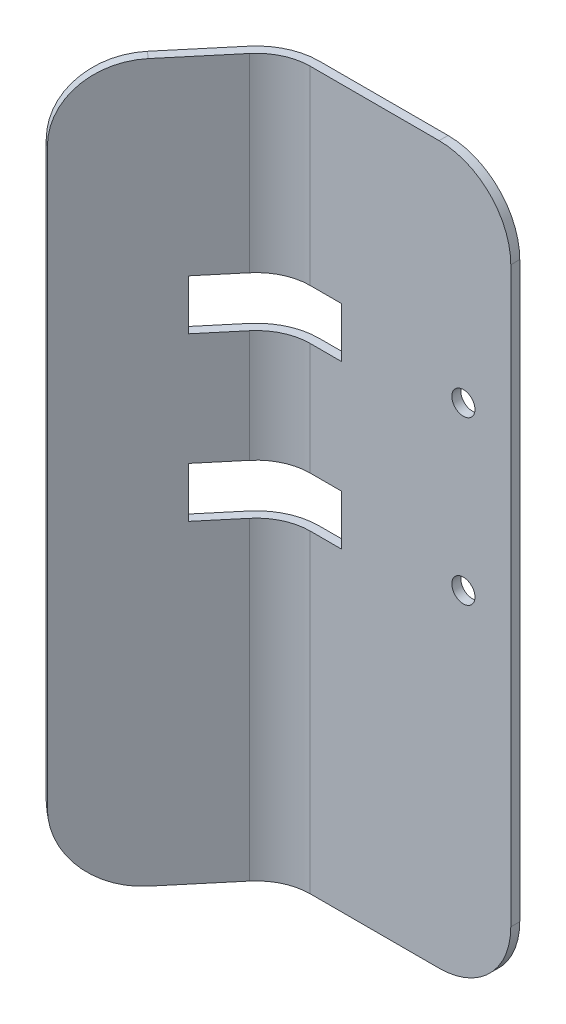
SolidWorks part; units mm, degrees
ref_plane "Front Plane" through (0, 0, 0) normal (0, 0, 1) x (1, 0, 0)
ref_plane "Top Plane" through (0, 0, 0) normal (0, 1, 0) x (1, 0, 0)
ref_plane "Right Plane" through (0, 0, 0) normal (1, 0, 0) x (0, 0, -1)
other "Bounding Box"
ref_plane "Default Plane" through (13.8565, 3.175, 6.7999) normal (0, -1, 0) x (-1, 0, 0)
sketch "Sketch1" plane through (0, 0, 0) normal (0, 1, 0) x (1, 0, 0)
  line L0 (0, 0) -> (-35.56, 0)
  line L1 (-42.8566, -3.4024) -> (-59.217, -22.9)
  line L2 (0, 1.5875) -> (-35.56, 1.5875)
  line L3 (-44.0727, -2.382) -> (-60.4331, -21.8796)
  line L4 (-60.4331, -21.8796) -> (-59.217, -22.9)
  line L5 (0, 1.5875) -> (0, 0)
  arc A0 (-35.56, 0) -> (-42.8566, -3.4024) centre (-35.56, -9.525) ccw
  arc A1 (-35.56, 1.5875) -> (-44.0727, -2.382) centre (-35.56, -9.525) ccw
  point P11 (-64.9523, -7.3771)
  point P12 (-61.4052, -4.5354)
  dimension "D5" = 9.525
  dimension "D2" = 35.56
  dimension "D3" = 22.9
  dimension "D4" = 130
  dimension "D1" = 1.5875
extrude "Boss-Extrude1" add sketch "Sketch1" along normal blind 127
sketch "Sketch2" plane through (0, 0, -1.5875) normal (0, 0, -1) x (-1, 0, 0)
  line L0 (8.4, 60.1161) -> (8.4, 88.9) construction
  line L1 (8.4, 88.9) -> (40.4616, 88.9) construction
  line L2 (40.4616, 88.9) -> (40.4616, 60.1161) construction
  line L3 (40.4616, 60.1161) -> (8.4, 60.1161) construction
  line L7 (0, 127) -> (35.56, 127) construction
  line L9 (0, 127) -> (0, 0) construction
  line L11 (29.99, 84.455) -> (49.04, 84.455)
  line L12 (29.99, 84.455) -> (29.99, 93.345)
  line L13 (29.99, 93.345) -> (49.04, 93.345)
  line L14 (49.04, 84.455) -> (49.04, 93.345)
  line L15 (29.99, 84.455) -> (49.04, 93.345) construction
  line L16 (29.99, 93.345) -> (49.04, 84.455) construction
  line L17 (29.99, 55.6711) -> (49.04, 55.6711)
  line L18 (29.99, 55.6711) -> (29.99, 64.5611)
  line L19 (29.99, 64.5611) -> (49.04, 64.5611)
  line L20 (49.04, 55.6711) -> (49.04, 64.5611)
  line L21 (29.99, 55.6711) -> (49.04, 64.5611) construction
  line L22 (29.99, 64.5611) -> (49.04, 55.6711) construction
  circle A0 centre (40.4616, 60.1161) radius 2.05 construction
  circle A1 centre (40.4616, 88.9) radius 2.05 construction
  circle A2 centre (8.4, 88.9) radius 2.05
  circle A3 centre (8.4, 60.1161) radius 2.05
  point P12 (39.515, 88.9)
  point P17 (39.515, 60.1161)
  point P22 (24.8584, 47.4161)
  point P23 (19.1648, 72.5709)
  dimension "D3" = 4.1
  dimension "D1" = 28.7839
  dimension "D2" = 32.0616
  dimension "D4" = 38.1
  dimension "D5" = 6.35
  dimension "D6" = 8.89
  dimension "D8" = 19.05
  dimension "D7" = 21.59
extrude "Cut-Extrude1" cut sketch "Sketch2" against normal through all
fillet "Fillet1" radius 12.7 4 edges at (-59.825, 127, 22.3898) (-59.825, 0, 22.3898) (0, 127, -0.7937) (0, 0, -0.7937)
sketch "Sketch4" plane through (-23.4739, 0, -19.6969) normal (0.766, 0, 0.6428) x (0.6428, 0, -0.766)
  line L0 (-39.7738, 93.345) -> (-37.8819, 93.345) construction
  line L1 (-39.7738, 84.455) -> (-39.7738, 93.345) construction
  line L2 (-39.7738, 84.455) -> (-37.8819, 84.455) construction
  line L3 (-37.8819, 93.345) -> (-37.8819, 84.455) construction
  line L4 (-39.7738, 55.6711) -> (-37.8819, 55.6711) construction
  line L5 (-39.7738, 55.6711) -> (-39.7738, 64.5611) construction
  line L6 (-37.8819, 64.5611) -> (-37.8819, 55.6711) construction
  line L7 (-39.7738, 64.5611) -> (-37.8819, 64.5611) construction
  line L8 (-39.7738, 93.345) -> (-37.8819, 93.345)
  line L9 (-39.7738, 84.455) -> (-39.7738, 93.345)
  line L10 (-39.7738, 84.455) -> (-37.8819, 84.455)
  line L11 (-37.8819, 93.345) -> (-37.8819, 84.455)
  line L12 (-39.7738, 55.6711) -> (-37.8819, 55.6711)
  line L13 (-39.7738, 55.6711) -> (-39.7738, 64.5611)
  line L14 (-37.8819, 64.5611) -> (-37.8819, 55.6711)
  line L15 (-39.7738, 64.5611) -> (-37.8819, 64.5611)
extrude "Boss-Extrude2" add sketch "Sketch4" against normal up to surface up to face at (-49.04, 88.9, 9.5367)
equation "\"D3@Sketch2\"=4.1mm"
equation "\"D3@Sketch1\"=1.000in-2.5mm"
